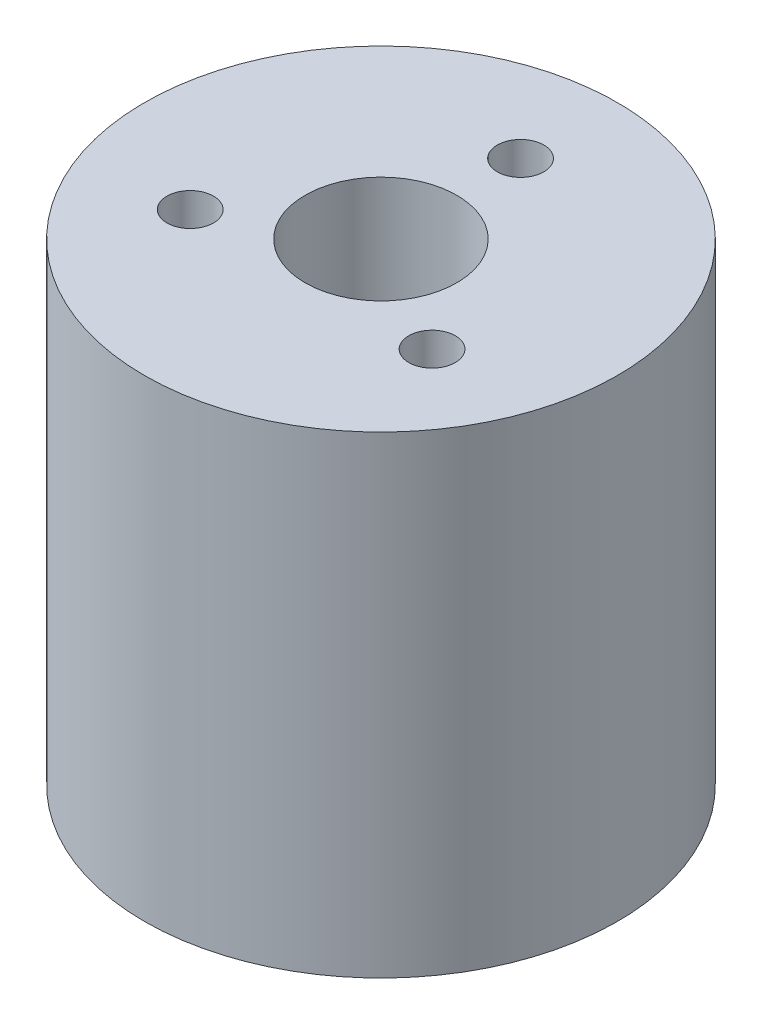
SolidWorks part; units mm, degrees
ref_plane "Front Plane" through (0, 0, 0) normal (0, 0, 1) x (1, 0, 0)
ref_plane "Top Plane" through (0, 0, 0) normal (0, 1, 0) x (1, 0, 0)
ref_plane "Right Plane" through (0, 0, 0) normal (1, 0, 0) x (0, 0, -1)
sketch "Sketch1" plane through (0, 0, 0) normal (0, 1, 0) x (1, 0, 0)
  circle A0 centre (0, 0) radius 12.7
  dimension "D1" = 25.4
extrude "Boss-Extrude1" add sketch "Sketch1" along normal blind 25.4
sketch "Sketch2" plane through (0, 25.4, 0) normal (0, 1, 0) x (1, 0, 0)
  circle A0 centre (0, 0) radius 4.075
  dimension "D1" = 8.15
extrude "Cut-Extrude1" cut sketch "Sketch2" against normal blind 19.05
sketch "Sketch3" plane through (0, 25.4, 0) normal (0, 1, 0) x (1, 0, 0)
  circle A0 centre (0, 0) radius 7.5 construction
  circle A1 centre (0, 7.5) radius 1.25
  circle A2 centre (6.4952, -3.75) radius 1.25
  circle A3 centre (-6.4952, -3.75) radius 1.25
  point P12 (0, 0)
  dimension "D2" = 15
  dimension "D3" = 2.5
  dimension "D1" = 3
extrude "Cut-Extrude2" cut sketch "Sketch3" against normal blind 10 contours A3 | A2 | A1
